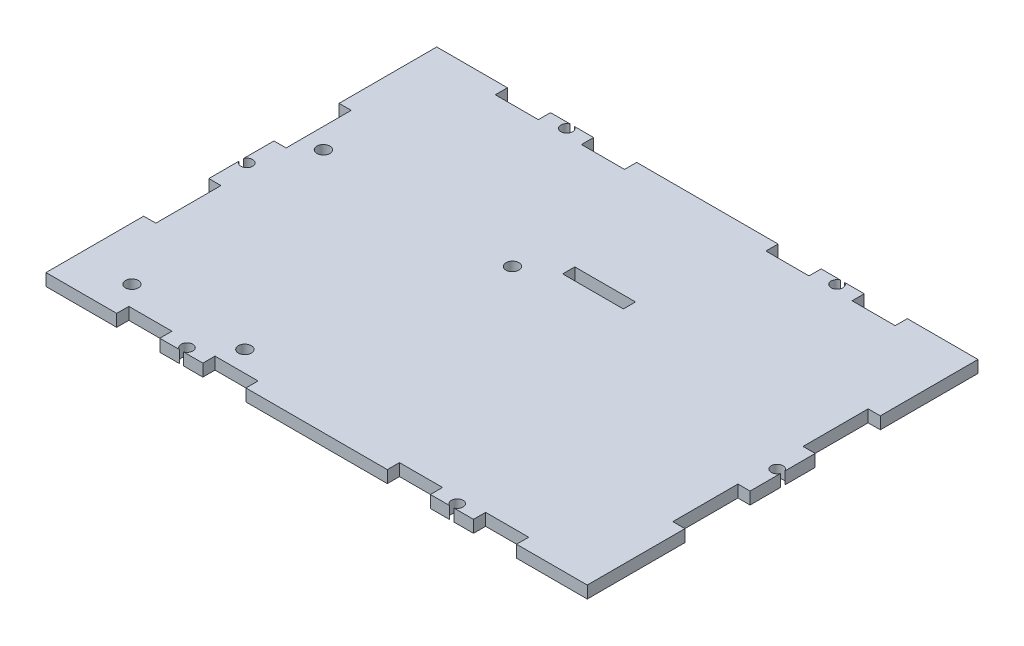
SolidWorks part; units mm, degrees
ref_plane "Front Plane" through (0, 0, 0) normal (0, 0, 1) x (1, 0, 0)
ref_plane "Top Plane" through (0, 0, 0) normal (0, 1, 0) x (1, 0, 0)
ref_plane "Right Plane" through (0, 0, 0) normal (1, 0, 0) x (0, 0, -1)
sketch "Sketch1" plane through (0, 0, 0) normal (0, 1, 0) x (1, 0, 0)
  line L1 (-66.85, 48.26) -> (66.85, 48.26)
  line L2 (-66.85, 48.26) -> (-66.85, -48.26)
  line L3 (-66.85, -48.26) -> (66.85, -48.26)
  line L4 (66.85, 48.26) -> (66.85, -48.26)
  line L5 (-66.85, 48.26) -> (66.85, -48.26) construction
  line L6 (-66.85, -48.26) -> (66.85, 48.26) construction
  point P0 (0, 0)
  dimension "D1" = 133.7
  dimension "D2" = 96.52
extrude "Boss-Extrude2" add sketch "Sketch1" along normal blind 3 contours L1 L4 L3 L2
sketch "Sketch6" plane through (-66.85, 0, 0) normal (-1, 0, 0) x (0, 0, 1)
  line L0 (-48.26, 3) -> (48.26, 3) construction
  line L5 (-48.26, 0) -> (48.26, 0) construction
  line L10 (-24.13, 3) -> (24.13, 3)
  line L11 (-24.13, 3) -> (-24.13, 0)
  line L12 (-24.13, 0) -> (24.13, 0)
  line L13 (24.13, 3) -> (24.13, 0)
  point P0 (0, 0)
  point P10 (0, 0)
  dimension "D1" = 48.26
extrude "Cut-Extrude2" cut sketch "Sketch6" against normal blind 3
mirror "Mirror3" about plane through (0, 0, 0) normal (1, 0, 0) of "Cut-Extrude2"
sketch "Sketch9" plane through (63.85, 0, 0) normal (1, 0, 0) x (0, 0, -1)
  line L0 (24.13, 0) -> (-24.13, 0) construction
  line L1 (8.0433, 0) -> (-8.0433, 0)
  line L2 (8.0433, 0) -> (8.0433, 3)
  line L3 (8.0433, 3) -> (-8.0433, 3)
  line L4 (-8.0433, 0) -> (-8.0433, 3)
  line L5 (-24.13, 3) -> (24.13, 3) construction
  point P6 (0, 3)
  point P9 (0, 3)
  dimension "D1" = 16.0867
extrude "Boss-Extrude4" add sketch "Sketch9" along normal blind 3
mirror "Mirror5" about plane through (0, 0, 0) normal (1, 0, 0) of "Boss-Extrude4"
sketch "Sketch11" plane through (0, 0, 48.26) normal (0, 0, 1) x (1, 0, 0)
  line L5 (-17.4625, 3) -> (-49.3875, 3)
  line L6 (-17.4625, 3) -> (-17.4625, 0)
  line L7 (-17.4625, 0) -> (-49.3875, 0)
  line L8 (-49.3875, 3) -> (-49.3875, 0)
  dimension "D1" = 31.925
extrude "Cut-Extrude8" cut sketch "Sketch11" against normal blind 3
sketch "Sketch15" plane through (0, 0, 45.26) normal (0, 0, 1) x (1, 0, 0)
  line L0 (-49.3875, 0) -> (-17.4625, 0) construction
  line L1 (-38.7458, 3) -> (-28.1042, 3)
  line L2 (-38.7458, 3) -> (-38.7458, 0)
  line L3 (-38.7458, 0) -> (-28.1042, 0)
  line L4 (-28.1042, 3) -> (-28.1042, 0)
  line L5 (-17.4625, 3) -> (-49.3875, 3) construction
  point P6 (-33.425, 3)
  point P9 (-33.425, 3)
  dimension "D1" = 10.6417
extrude "Boss-Extrude7" add sketch "Sketch15" along normal blind 3
mirror "Mirror11" about plane through (0, 0, 0) normal (0, 0, 1) of "Cut-Extrude8"
mirror "Mirror12" about plane through (0, 0, 0) normal (0, 0, 1) of "Boss-Extrude7"
sketch "Sketch18" plane through (0, 0, 48.26) normal (0, 0, 1) x (1, 0, 0)
  line L0 (-17.4625, 0) -> (66.85, 0) construction
  line L5 (49.3875, 0) -> (17.4625, 0)
  line L6 (49.3875, 0) -> (49.3875, 3)
  line L7 (49.3875, 3) -> (17.4625, 3)
  line L8 (17.4625, 0) -> (17.4625, 3)
  line L10 (0, 0) -> (66.85, 0) construction
  line L12 (0, 0) -> (66.85, 0)
  line L13 (0, 0) -> (0, 3)
  line L14 (0, 3) -> (66.85, 3)
  line L15 (66.85, 0) -> (66.85, 3)
  point P2 (33.425, 3)
  point P3 (33.425, 3)
  line M1 (66.85, 3) -> (-17.4625, 3)
  line M3 (-17.4625, 0) -> (66.85, 0)
  dimension "D1" = 31.925
extrude "Cut-Extrude10" cut sketch "Sketch18" against normal blind 3 contours L8 L6 M3 M1
sketch "Sketch19" plane through (0, 0, 45.26) normal (0, 0, 1) x (1, 0, 0)
  line L0 (49.3875, 3) -> (17.4625, 3) construction
  line L1 (28.1042, 3) -> (38.7458, 3)
  line L2 (28.1042, 3) -> (28.1042, 0)
  line L3 (28.1042, 0) -> (38.7458, 0)
  line L4 (38.7458, 3) -> (38.7458, 0)
  line L5 (17.4625, 0) -> (49.3875, 0) construction
  point P4 (33.425, 3)
  point P7 (33.425, 3)
  point P8 (33.425, 0)
  point P11 (33.425, 0)
  dimension "D1" = 10.6417
sketch "Sketch20" plane through (0, 0, 45.26) normal (0, 0, 1) x (1, 0, 0)
extrude "Boss-Extrude8" add sketch "Sketch19" along normal blind 3
mirror "Mirror13" about plane through (0, 0, 0) normal (0, 0, 1) of "Cut-Extrude10"
mirror "Mirror14" about plane through (0, 0, 0) normal (0, 0, 1) of "Boss-Extrude8"
sketch "Sketch21" plane through (0, 3, 0) normal (0, 1, 0) x (1, 0, 0)
  line L0 (38.7458, -48.26) -> (28.1042, -48.26) construction
  line L1 (31.8758, -48.36) -> (34.8758, -48.36)
  line L2 (31.8758, -48.36) -> (31.8758, -45.26)
  line L3 (31.8758, -45.26) -> (34.8758, -45.26)
  line L4 (34.8758, -48.36) -> (34.8758, -45.26)
  line L5 (38.7458, -48.26) -> (38.7458, -45.26) construction
  circle A0 centre (33.3758, -46.91) radius 1.45
  point P12 (33.3758, -45.26)
  dimension "D3" = 2.9
  dimension "D1" = 3
  dimension "D2" = 3.1
  dimension "D4" = 0.1
  dimension "D5" = 3.87
extrude "Cut-Extrude11" cut sketch "Sketch21" against normal blind 3 contours A0 L4
mirror "Mirror15" about plane through (0, 0, 0) normal (0, 0, 1) of "Cut-Extrude11"
mirror "Mirror16" about plane through (0, 0, 0) normal (1, 0, 0) of "Mirror15", "Cut-Extrude11"
sketch "Sketch22" plane through (0, 3, 0) normal (0, 1, 0) x (1, 0, 0)
  line L1 (66.95, -1.5) -> (63.85, -1.5)
  line L2 (66.95, -1.5) -> (66.95, 1.5)
  line L3 (66.95, 1.5) -> (63.85, 1.5)
  line L4 (63.85, -1.5) -> (63.85, 1.5)
  circle A0 centre (65.5, 0) radius 1.45
  dimension "D3" = 2.9
  dimension "D1" = 3
  dimension "D2" = 3.1
extrude "Cut-Extrude19" cut sketch "Sketch22" against normal blind 3 contours A0
mirror "Mirror17" about plane through (0, 0, 0) normal (1, 0, 0) of "Cut-Extrude19"
sketch "Sketch24" plane through (0, 3, 0) normal (0, 1, 0) x (1, 0, 0)
  line L0 (-10.55, 12.26) -> (-58.85, 12.26) construction
  line L2 (-63.85, 8.0433) -> (-63.85, 24.13) construction
  line L3 (-38.7458, 45.26) -> (-49.3875, 45.26) construction
  circle A0 centre (-53.75, -40.14) radius 1.6
  circle A1 centre (-25.85, -40.14) radius 1.6
  circle A2 centre (-10.55, 10.66) radius 1.6
  circle A3 centre (-58.85, 12.26) radius 1.6
  dimension "D2" = 33
  dimension "D4" = 3.2
  dimension "D5" = 50.8
  dimension "D6" = 48.3
  dimension "D8" = 27.9
  dimension "D7" = 5.1
  dimension "D10" = 5
extrude "Cut-Extrude20" cut sketch "Sketch24" against normal blind 3
sketch "Sketch25" plane through (0, 3, 0) normal (0, 1, 0) x (1, 0, 0)
  line L0 (-17.4625, 48.26) -> (17.4625, 48.26) construction
  line L1 (-2.75, 18.26) -> (12.25, 18.26)
  line L2 (-2.75, 18.26) -> (-2.75, 15.26)
  line L3 (-2.75, 15.26) -> (12.25, 15.26)
  line L4 (12.25, 18.26) -> (12.25, 15.26)
  line L6 (-66.85, 48.26) -> (-66.85, 24.13) construction
  dimension "D1" = 3
  dimension "D2" = 15
  dimension "D3" = 30
  dimension "D4" = 79.1
extrude "Cut-Extrude21" cut sketch "Sketch25" against normal blind 3
